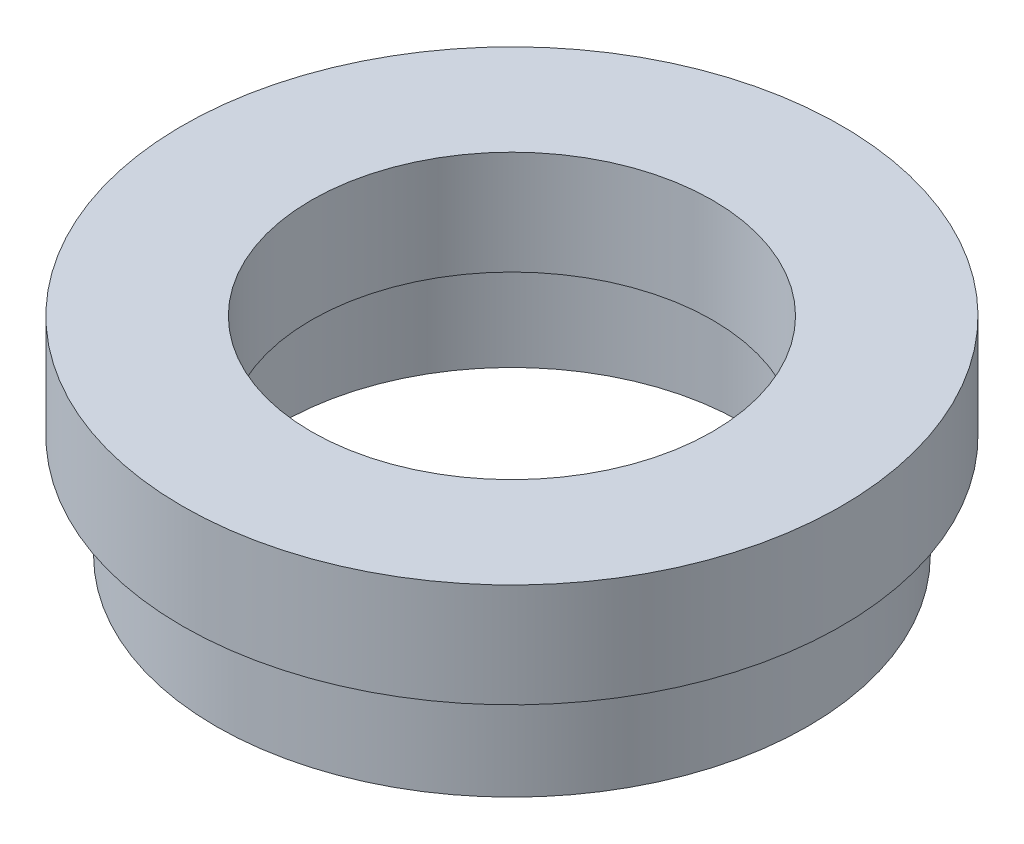
SolidWorks part; units mm, degrees
ref_plane "前视基准面" through (0, 0, 0) normal (0, 0, 1) x (1, 0, 0)
ref_plane "上视基准面" through (0, 0, 0) normal (0, 1, 0) x (1, 0, 0)
ref_plane "右视基准面" through (0, 0, 0) normal (1, 0, 0) x (0, 0, -1)
sketch "草图1" plane through (0, 0, 0) normal (0, 0, 1) x (1, 0, 0)
  line L0 (0, 13.7447) -> (0, -18.6809) construction
  line L1 (14.25, 0) -> (11.1, 0)
  line L2 (11.1, 0) -> (11.1, 4)
  line L3 (11.1, 4) -> (11.7, 4)
  line L4 (11.7, 4) -> (11.7, 5)
  line L5 (11.7, 5) -> (9.66, 5)
  line L6 (9.66, 5) -> (9.66, 10)
  line L7 (9.66, 10) -> (15.875, 10)
  line L8 (15.875, 10) -> (15.875, 5)
  line L9 (15.875, 5) -> (13.75, 5)
  line L10 (13.75, 5) -> (13.75, 4)
  line L11 (13.75, 4) -> (14.25, 4)
  line L12 (14.25, 4) -> (14.25, 0)
  dimension "D1" = 10
  dimension "D2" = 15.875
  dimension "D3" = 9.66
  dimension "D4" = 11.1
  dimension "D5" = 11.7
  dimension "D6" = 14.25
  dimension "D7" = 13.75
  dimension "D8" = 1
  dimension "D9" = 1
  dimension "D10" = 5
  dimension "D11" = 5
revolve "旋转1" add sketch "草图1" angle 360 about L0
cosmetic thread "装饰螺纹线1" parameters "D2"=20.32
cosmetic thread "装饰螺纹线2" parameters "D2"=23.2
cosmetic thread "装饰螺纹线3" parameters "D2"=27.5
